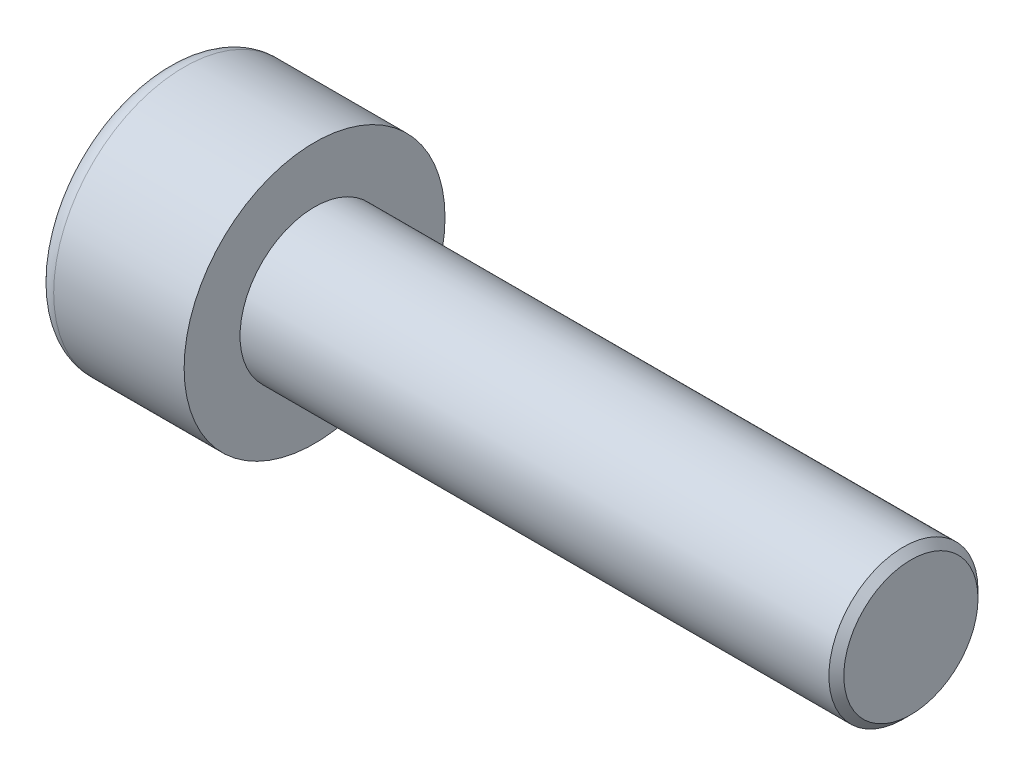
SolidWorks part; units mm, degrees
ref_plane "Front" through (0, 0, 0) normal (0, 0, 1) x (1, 0, 0)
ref_plane "Top" through (0, 0, 0) normal (0, 1, 0) x (1, 0, 0)
ref_plane "Right" through (0, 0, 0) normal (1, 0, 0) x (0, 0, -1)
sketch "Sketch1" plane through (0, 0, 0) normal (1, 0, 0) x (0, 0, -1)
  circle A0 centre (0, 0) radius 3.5
  dimension "dk" = 7
extrude "BaseHead" add sketch "Sketch1" along normal blind 4
sketch "Sketch2" plane through (4, 0, 0) normal (1, 0, 0) x (0, 0, -1)
  circle A0 centre (0, 0) radius 2
  dimension "d" = 4
extrude "BaseBody" add sketch "Sketch2" along normal blind 16
cosmetic thread "ThreadCosmetic1" parameters "b"=16, "D2"=3.242
sketch "Sketch3" plane through (0, 0, 0) normal (1, 0, 0) x (0, 0, -1)
  line L1 (1.7321, 0) -> (0.866, 1.5)
  line L2 (0.866, 1.5) -> (-0.866, 1.5)
  line L3 (-0.866, 1.5) -> (-1.7321, 0)
  line L4 (-1.7321, 0) -> (-0.866, -1.5)
  line L5 (-0.866, -1.5) -> (0.866, -1.5)
  line L6 (0.866, -1.5) -> (1.7321, 0)
  circle A0 centre (0, 0) radius 1.5 construction
  dimension "s" = 3
  dimension "e" = 3.4641
extrude "HexagonSocket" cut sketch "Sketch3" along normal blind 2
sketch "Sketch4" plane through (-4.1961, 0.75, 0) normal (0, 0, 1) x (-1, 0, 0)
  line L0 (-6.1961, 2.25) -> (-7.0622, 0.75)
  line L2 (-7.0622, 0.75) -> (-6.1961, 0.75)
  line L3 (-6.1961, 0.75) -> (-6.1961, 2.25)
  line L4 (-5.0351, 0.75) -> (0.839, 0.75) construction
  line L5 (-24.1961, 0.75) -> (-8.1961, 0.75) construction
  line L6 (-8.1961, 0.75) -> (-4.1961, 0.75) construction
  dimension "m" = 60
revolve "Cut-Revolve1" cut sketch "Sketch4" angle 360 about L4
fillet "HeadFillet" [suppressed] radius 0.2
fillet "TopFillet" radius 0.5 1 edges at (0, 0, -3.5)
chamfer "Chamfer1" distance 0.2 angle 45 1 edges at (20, 0, -2)
sketch "Sketch5" plane through (0, 0, 0) normal (0, 0, 1) x (1, 0, 0)
  line L0 (19.8, 1.6718) -> (19.9895, 2)
  line L1 (19.9895, 2) -> (19.9895, 2.379)
  line L2 (19.9895, 2.379) -> (19.6105, 2.379)
  line L3 (19.6105, 2.379) -> (19.6105, 2)
  line L4 (19.6105, 2) -> (19.8, 1.6718)
  line L5 (0, 0) -> (7.8886, 0) construction
  line L6 (19.8, -2) -> (19.8, 2) construction
  dimension "D1" = 4
  dimension "D2" = 0.379
revolve "Cut-Revolve10" [suppressed] cut sketch "Sketch5" angle 360 about L5
pattern_linear "LPattern10" [suppressed] count 35 spacing 0.4548 along (1, 0, 0)
equation "\"r1@TopFillet\" = \"d@Sketch2\" / 8"
equation "\"D1@Chamfer1\" = \"r@HeadFillet\""
equation "\"D1@Sketch5\" = \"d@Sketch2\""
equation "\"D2@Sketch5\" =  ( \"d@Sketch2\" - \"D2@ThreadCosmetic1\" )  / 2"
equation "\"D3@LPattern10\" = \"D2@Sketch5\" * 1.2"
equation "\"D1@LPattern10\" = \"b@ThreadCosmetic1\" / \"D3@LPattern10\""
